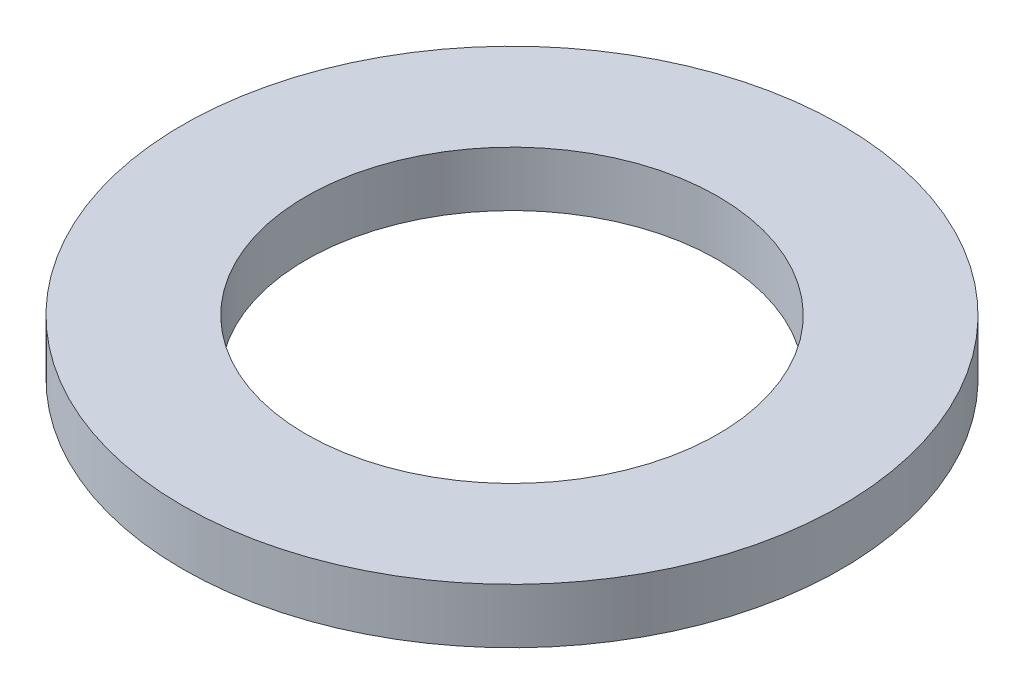
SolidWorks part; units mm, degrees
ref_plane "Front Plane" through (0, 0, 0) normal (0, 0, 1) x (1, 0, 0)
ref_plane "Top Plane" through (0, 0, 0) normal (0, 1, 0) x (1, 0, 0)
ref_plane "Right Plane" through (0, 0, 0) normal (1, 0, 0) x (0, 0, -1)
sketch "Sketch1" plane through (0, 0, 0) normal (0, 1, 0) x (1, 0, 0)
  circle A0 centre (0, 0) radius 6
  dimension "D1" = 12
extrude "Boss-Extrude1" add sketch "Sketch1" along normal blind 1
sketch "Sketch2" plane through (0, 1, 0) normal (0, 1, 0) x (1, 0, 0)
  circle A0 centre (0, 0) radius 3.75
  dimension "D1" = 7.5
extrude "Cut-Extrude1" cut sketch "Sketch2" against normal up to next
